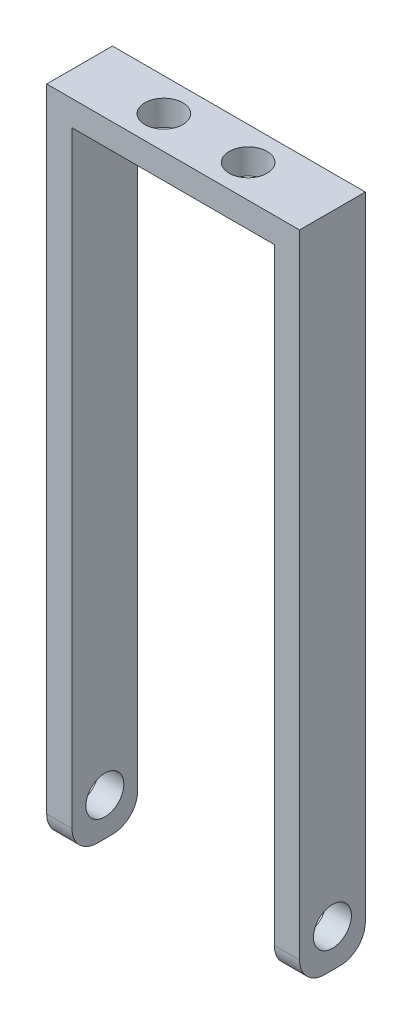
SolidWorks part; units mm, degrees
ref_plane "Front Plane" through (0, 0, 0) normal (0, 0, 1) x (1, 0, 0)
ref_plane "Top Plane" through (0, 0, 0) normal (0, 1, 0) x (1, 0, 0)
ref_plane "Right Plane" through (0, 0, 0) normal (1, 0, 0) x (0, 0, -1)
sketch "Sketch1" plane through (0, 0, 0) normal (0, 1, 0) x (1, 0, 0)
  line L1 (-15, -3.9) -> (15, -3.9)
  line L2 (-15, -3.9) -> (-15, 3.9)
  line L3 (-15, 3.9) -> (15, 3.9)
  line L4 (15, -3.9) -> (15, 3.9)
  line L5 (-15, -3.9) -> (15, 3.9) construction
  line L6 (-15, 3.9) -> (15, -3.9) construction
  point P0 (0, 0)
  dimension "D1" = 7.8
  dimension "D2" = 30
extrude "Boss-Extrude1" add sketch "Sketch1" against normal blind 3
sketch "Sketch2" plane through (0, 0, 0) normal (0, 1, 0) x (1, 0, 0)
  line L0 (-5, 0) -> (5, 0) construction
  circle A0 centre (-5, 0) radius 2.25
  circle A1 centre (5, 0) radius 2.25
  point P4 (0, 0)
extrude "Cut-Extrude1" cut sketch "Sketch2" against normal up to next
sketch "Sketch3" plane through (0, -3, 0) normal (0, -1, 0) x (1, 0, 0)
  line L0 (15, -3.9) -> (-15, -3.9) construction
  line L1 (-15, 3.9) -> (-12, 3.9)
  line L2 (-15, 3.9) -> (-15, -3.9)
  line L3 (-15, -3.9) -> (-12, -3.9)
  line L4 (-12, 3.9) -> (-12, -3.9)
  line L6 (15, 3.9) -> (12, 3.9)
  line L7 (15, 3.9) -> (15, -3.9)
  line L8 (15, -3.9) -> (12, -3.9)
  line L9 (12, 3.9) -> (12, -3.9)
  dimension "D1" = 3
  dimension "D2" = 3
extrude "Boss-Extrude2" add sketch "Sketch3" along normal blind 75
sketch "Sketch4" plane through (15, 0, 0) normal (1, 0, 0) x (0, 0, -1)
  line L0 (0, -78) -> (0, -73.5) construction
  line L1 (3.9, -78) -> (-3.9, -78) construction
  circle A1 centre (0, -73.5) radius 2.25
extrude "Cut-Extrude2" cut sketch "Sketch4" against normal through all both and the other way through all
fillet "Fillet1" radius 3 4 edges at (-13.5, -78, -3.9) (13.5, -78, -3.9) (-13.5, -78, 3.9) (13.5, -78, 3.9)
